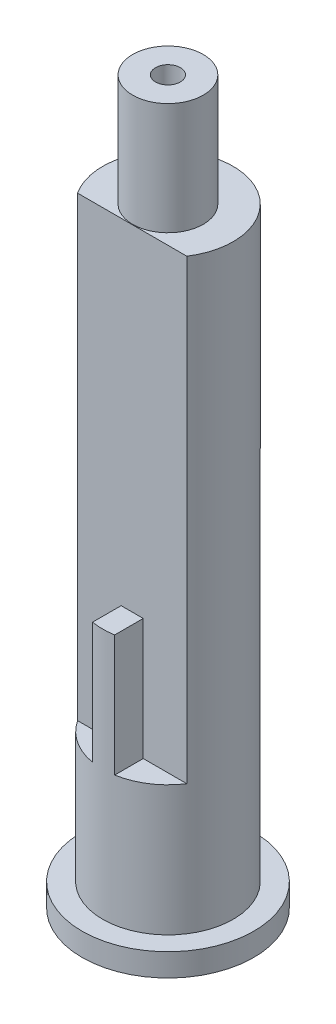
SolidWorks part; units mm, degrees
ref_plane "Front Plane" through (0, 0, 0) normal (0, 0, 1) x (1, 0, 0)
ref_plane "Top Plane" through (0, 0, 0) normal (0, 1, 0) x (1, 0, 0)
ref_plane "Right Plane" through (0, 0, 0) normal (1, 0, 0) x (0, 0, -1)
sketch "Sketch1" plane through (0, 0, 0) normal (0, 1, 0) x (1, 0, 0)
  circle A0 centre (0, 0) radius 6.255
  dimension "D1" = 12.51
extrude "Bottom Ring" add sketch "Sketch1" along normal blind 1.66
sketch "Sketch2" plane through (0, 0, 0) normal (0, 1, 0) x (1, 0, 0)
  circle A0 centre (0, 0) radius 4.755
  dimension "D1" = 9.51
extrude "Main Cylinder" add sketch "Sketch2" along normal blind 44.41
sketch "Sketch3" plane through (0, 0, 0) normal (0, 1, 0) x (1, 0, 0)
  circle A0 centre (0, 0) radius 2.57
  dimension "D1" = 5.14
extrude "Top Cylinder" add sketch "Sketch3" along normal blind 52.56
ref_plane "Top Main Cyl. Ref." through (0, 44.41, 0) normal (0, 1, 0) x (1, 0, 0)
sketch "Sketch4" plane through (0, 44.41, 0) normal (0, 1, 0) x (1, 0, 0)
  line L0 (0, 4.755) -> (10.4547, 4.755) construction
  line L1 (0, -6.8805) -> (0, 6.8805) construction
  line L2 (-0.805, -2.605) -> (-0.805, -4.6864)
  line L9 (-3.9779, -2.605) -> (-0.805, -2.605)
  line L11 (0.805, -2.605) -> (0.805, -4.6864)
  line L12 (0.805, -2.605) -> (3.9779, -2.605)
  circle A0 centre (0, 0) radius 4.755 construction
  arc A1 (0.805, -4.6864) -> (3.9779, -2.605) centre (0, 0) ccw
  circle A2 centre (0, 0) radius 4.755 construction
  arc A3 (-3.9779, -2.605) -> (-0.805, -4.6864) centre (0, 0) ccw
  dimension "D1" = 7.36
  dimension "D2" = 0.805
  dimension "D3" = 0.805
extrude "Cutout pt1" cut sketch "Sketch4" against normal blind 33.28
sketch "Sketch5" plane through (0, 44.41, 0) normal (0, 1, 0) x (1, 0, 0)
  line L0 (-0.805, -2.605) -> (-0.805, -4.6864)
  line L1 (0.805, -2.605) -> (0.805, -4.6864)
  line L2 (-0.805, -2.605) -> (0.805, -2.605)
  arc A0 (-0.805, -4.6864) -> (0.805, -4.6864) centre (0, 0) ccw
  arc A1 (3.9779, -2.605) -> (-3.9779, -2.605) centre (0, 0) ccw construction
extrude "Cutout pt2" cut sketch "Sketch5" against normal blind 24.44
sketch "Sketch6" plane through (0, 0, 0) normal (0, 1, 0) x (1, 0, 0)
  circle A0 centre (0, 0) radius 3.47
  dimension "D1" = 6.94
extrude "Bottom Hole pt1" cut sketch "Sketch6" along normal blind 8.82
sketch "Sketch7" plane through (0, 52.56, 0) normal (0, 1, 0) x (1, 0, 0)
  circle A0 centre (0, 0) radius 0.905
  dimension "D1" = 1.81
extrude "Top Hole" cut sketch "Sketch7" against normal through all
sketch "Sketch8" plane through (0, 0, 0) normal (0, 1, 0) x (1, 0, 0)
  line L0 (0, 3.47) -> (8.0938, 3.47) construction
  line L1 (-3.3346, -0.96) -> (3.3346, -0.96)
  arc A0 (3.3346, -0.96) -> (-3.3346, -0.96) centre (0, 0) ccw
  circle A1 centre (0, 0) radius 3.47 construction
  dimension "D1" = 4.43
extrude "Bottom Hole pt2" cut sketch "Sketch8" along normal blind 43.23
